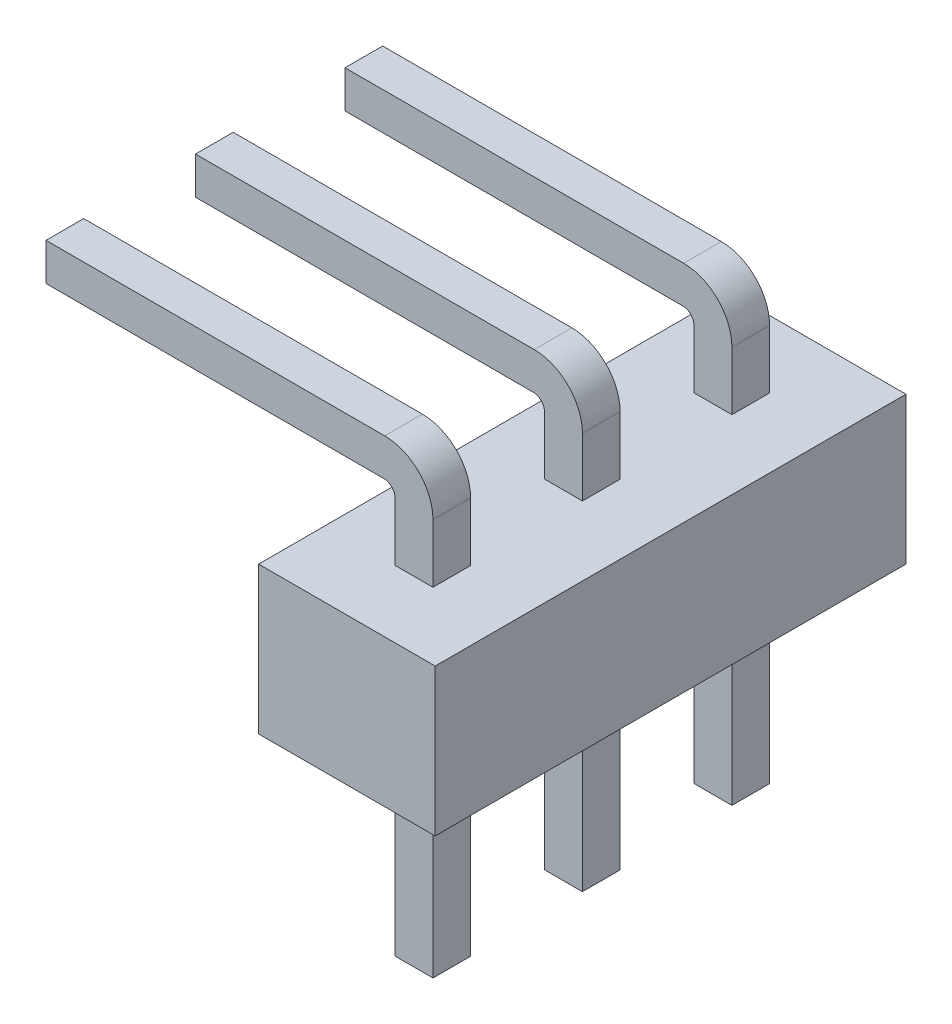
SolidWorks part; units mm, degrees
ref_plane "Front Plane" through (0, 0, 0) normal (0, 0, 1) x (1, 0, 0)
ref_plane "Top Plane" through (0, 0, 0) normal (0, 1, 0) x (1, 0, 0)
ref_plane "Right Plane" through (0, 0, 0) normal (1, 0, 0) x (0, 0, -1)
sketch "Sketch1" plane through (0, 0, 0) normal (0, 0, 1) x (1, 0, 0)
  line L0 (1.5, 0) -> (-1.5, 0) construction
  line L1 (-1.5, 1.25) -> (1.5, 1.25)
  line L2 (-1.5, 1.25) -> (-1.5, -1.25)
  line L3 (-1.5, -1.25) -> (1.5, -1.25)
  line L4 (1.5, 1.25) -> (1.5, -1.25)
  dimension "D1" = 3
  dimension "D2" = 2.5
extrude "Extrude1" add sketch "Sketch1" along normal mid plane 8
ref_plane "Plane4" through (0, 0, 2.86) normal (0, 0, 1) x (1, 0, 0)
sketch "Sketch2" plane through (0, 0, 2.86) normal (0, 0, 1) x (1, 0, 0)
  line L0 (-0.3225, 1.25) -> (-0.3225, 2.245)
  line L1 (1.5, 1.25) -> (-1.5, 1.25) construction
  line L2 (0.3225, 1.25) -> (0.3225, 2.245)
  line L3 (-0.3225, 1.25) -> (0.3225, 1.25)
  line L4 (0, 0) -> (0, 3.2035) construction
  line L5 (-0.5025, 2.4326) -> (-6.5025, 2.4326)
  line L6 (-6.5025, 2.4326) -> (-6.5025, 3.0683)
  line L7 (-6.5025, 3.0683) -> (-0.4975, 3.0683)
  line L8 (-0.3225, -1.25) -> (-0.3225, -4.75)
  line L9 (-1.5, -1.25) -> (1.5, -1.25) construction
  line L10 (-0.3225, -4.75) -> (0.3225, -4.75)
  line L11 (0.3225, -4.75) -> (0.3225, -1.25)
  line L12 (-0.3225, -1.25) -> (0.3225, -1.25)
  arc A0 (-0.3225, 2.245) -> (-0.5025, 2.4326) centre (-0.5103, 2.245) ccw
  arc A1 (0.3225, 2.245) -> (-0.4975, 3.0683) centre (-0.5008, 2.245) ccw
  dimension "D1" = 0.645
  dimension "D2" = 0.995
  dimension "D3" = 0.26
  dimension "D4" = 0.18
  dimension "D5" = 1.162
  dimension "D6" = 0.82
  dimension "D7" = 6
  dimension "D8" = 3.5
extrude "Extrude2" add sketch "Sketch2" against normal blind 0.64
pattern_linear "LPattern1" count 3 spacing 2.54 along (0, 0, -1) of "Extrude2"
chamfer "Chamfer1" distance 0.25 angle 45 24 edges at (-6.5025, 2.4326, 0) (-6.5025, 2.7505, -0.32) (-6.5025, 3.0683, 0) (-6.5025, 2.7505, 0.32) (0.3225, -4.75, 2.54) (0, -4.75, 2.22) (-0.3225, -4.75, 2.54) (0, -4.75, 2.86) (0.3225, -4.75, -2.54) (0, -4.75, -2.86) (-0.3225, -4.75, -2.54) (0, -4.75, -2.22) (0.3225, -4.75, 0) (0, -4.75, -0.32) (-0.3225, -4.75, 0) (0, -4.75, 0.32) (-6.5025, 2.4326, 2.54) (-6.5025, 2.7505, 2.22) (-6.5025, 3.0683, 2.54) (-6.5025, 2.7505, 2.86) (-6.5025, 2.4326, -2.54) (-6.5025, 2.7505, -2.86) (-6.5025, 3.0683, -2.54) (-6.5025, 2.7505, -2.22)
